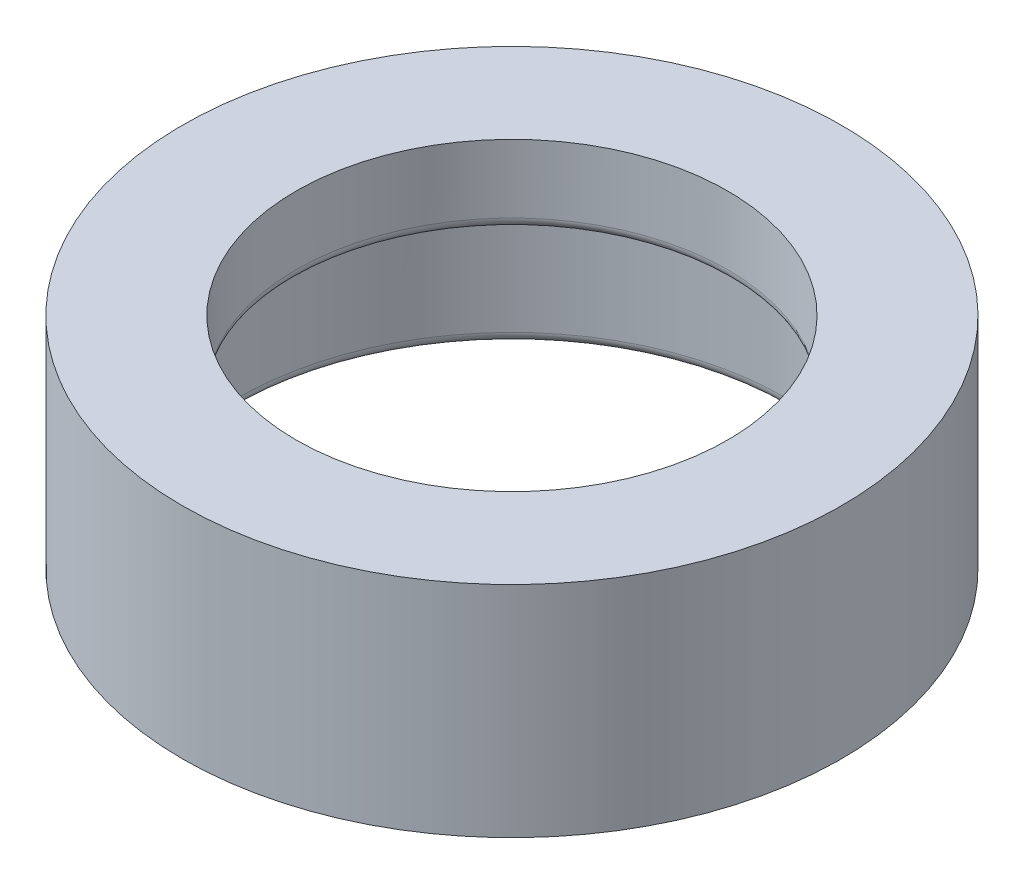
SolidWorks part; units mm, degrees
ref_plane "Front Plane" through (0, 0, 0) normal (0, 0, 1) x (1, 0, 0)
ref_plane "Top Plane" through (0, 0, 0) normal (0, 1, 0) x (1, 0, 0)
ref_plane "Right Plane" through (0, 0, 0) normal (1, 0, 0) x (0, 0, -1)
sketch "Sketch1" plane through (0, 0, 0) normal (0, 1, 0) x (1, 0, 0)
  circle A0 centre (0, 0) radius 30.55
extrude "Boss-Extrude1" add sketch "Sketch1" along normal blind 20.32
sketch "Sketch2" plane through (0, 0, 0) normal (0, -1, 0) x (1, 0, 0)
  circle A0 centre (0, 0) radius 25.404
extrude "Cut-Extrude1" cut sketch "Sketch2" against normal blind 13
sketch "Sketch3" plane through (0, 20.32, 0) normal (0, 1, 0) x (1, 0, 0)
  circle A0 centre (0, 0) radius 20
extrude "Cut-Extrude2" cut sketch "Sketch3" against normal through all
fillet "Fillet1" radius 1 1 edges at (0, 0, -25.404)
fillet "Fillet2" radius 1 1 edges at (0, 13, -20)
